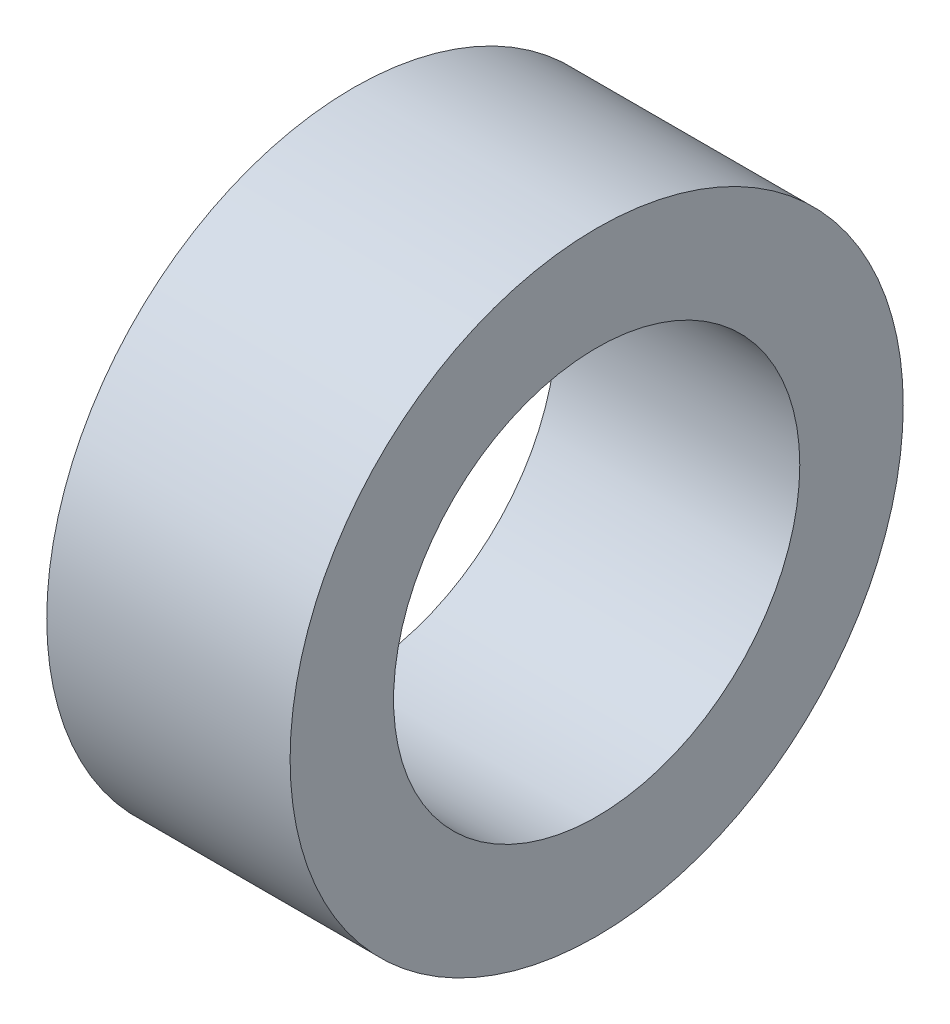
SolidWorks part; units mm, degrees
ref_plane "Front Plane" through (0, 0, 0) normal (0, 0, 1) x (1, 0, 0)
ref_plane "Top Plane" through (0, 0, 0) normal (0, 1, 0) x (1, 0, 0)
ref_plane "Right Plane" through (0, 0, 0) normal (1, 0, 0) x (0, 0, -1)
sketch "Sketch1" plane through (0, 0, 0) normal (1, 0, 0) x (0, 0, -1)
  circle A0 centre (0, 0) radius 2.65
  circle A1 centre (0, 0) radius 4
  dimension "D1" = 5.3
  dimension "D2" = 8
extrude "Boss-Extrude1" add sketch "Sketch1" along normal blind 3.175
